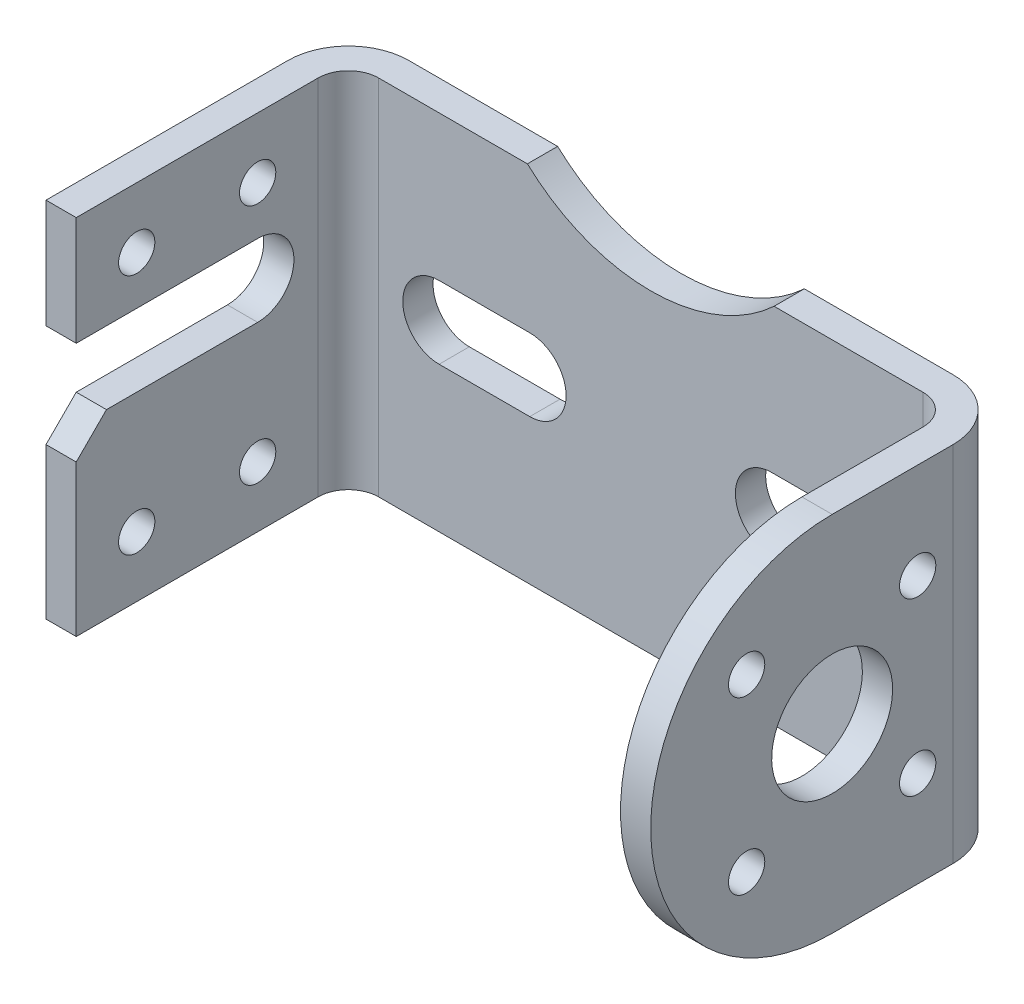
SolidWorks part; units mm, degrees
material "Nickel"
ref_plane "Front Plane" through (0, 0, 0) normal (0, 0, 1) x (1, 0, 0)
ref_plane "Top Plane" through (0, 0, 0) normal (0, 1, 0) x (1, 0, 0)
ref_plane "Right Plane" through (0, 0, 0) normal (1, 0, 0) x (0, 0, -1)
sketch "Sketch1" plane through (0, 0, 0) normal (0, 0, 1) x (1, 0, 0)
  line L1 (0, 0) -> (110, 0)
  line L2 (0, 0) -> (0, -60)
  line L3 (0, -60) -> (110, -60)
  line L4 (110, 0) -> (110, -60)
  dimension "D1" = 110
  dimension "D2" = 60
extrude "Boss-Extrude1" add sketch "Sketch1" along normal blind 50
sketch "Sketch2" plane through (0, 0, 50) normal (0, 0, 1) x (1, 0, 0)
  line L0 (110, 0) -> (0, 0) construction
  line L1 (5, 0) -> (105, 0)
  line L2 (5, 0) -> (5, -60)
  line L3 (5, -60) -> (105, -60)
  line L4 (105, 0) -> (105, -60)
  line L5 (0, -60) -> (110, -60) construction
  line L6 (110, -60) -> (110, 0) construction
  line L7 (0, 0) -> (0, -60) construction
  dimension "D1" = 5
  dimension "D2" = 5
extrude "Cut-Extrude1" cut sketch "Sketch2" against normal blind 45
fillet "Fillet1" radius 5 2 edges at (5, -30, 5) (105, -30, 5)
fillet "Fillet2" radius 10 2 edges at (110, -30, 0) (0, -30, 0)
sketch "Sketch3" plane through (0, 0, 5) normal (0, 0, 1) x (1, 0, 0)
  line L0 (100, 0) -> (10, 0) construction
  circle A0 centre (55, 22) radius 30
  dimension "D1" = 60
  dimension "D3" = 22
  dimension "D2" = 55
extrude "Cut-Extrude2" cut sketch "Sketch3" against normal through all
sketch "Sketch4" plane through (0, 0, 5) normal (0, 0, 1) x (1, 0, 0)
  line L0 (55, -8) -> (55, -70.5537) construction
  line L1 (20, -30) -> (35, -30) construction
  line L2 (20, -24) -> (35, -24)
  line L3 (20, -36) -> (35, -36)
  line L4 (10, -60) -> (100, -60) construction
  line L5 (90, -30) -> (75, -30) construction
  line L6 (90, -24) -> (75, -24)
  line L7 (90, -36) -> (75, -36)
  arc A0 (34.6039, 0) -> (75.3961, 0) centre (55, 22) ccw construction
  arc A1 (20, -24) -> (20, -36) centre (20, -30) ccw
  arc A2 (35, -36) -> (35, -24) centre (35, -30) ccw
  arc A3 (90, -24) -> (90, -36) centre (90, -30) cw
  arc A4 (75, -36) -> (75, -24) centre (75, -30) cw
  point P8 (27.5, -30)
  point P17 (82.5, -30)
  dimension "D3" = 6
  dimension "D1" = 15
  dimension "D2" = 20
  dimension "D4" = 30
extrude "Cut-Extrude3" cut sketch "Sketch4" against normal through all
sketch "Sketch5" plane through (0, 0, 0) normal (-1, 0, 0) x (0, 0, 1)
  line L0 (60, -24) -> (20, -24) construction
  line L1 (60, -30) -> (20, -30)
  line L2 (60, -18) -> (20, -18)
  line L3 (50, 0) -> (50, -60) construction
  line L5 (50, -30) -> (-1.733, -30) construction
  arc A0 (60, -30) -> (60, -18) centre (60, -24) ccw
  arc A1 (20, -18) -> (20, -30) centre (20, -24) ccw
  point P2 (40, -24)
  dimension "D1" = 6
  dimension "D2" = 30
  dimension "D3" = 40
extrude "Cut-Extrude4" cut sketch "Sketch5" against normal up to next
sketch "Sketch6" plane through (0, 0, 0) normal (-1, 0, 0) x (0, 0, 1)
  line L0 (30, 0) -> (30, -60) construction
  line L1 (50, 0) -> (10, 0) construction
  line L2 (50, -60) -> (10, -60) construction
  line L3 (0, -30) -> (52.0561, -30) construction
  line L4 (0, -60) -> (0, 0) construction
  line L5 (50, 0) -> (50, -18) construction
  circle A0 centre (20, -10) radius 3
  circle A1 centre (40, -10) radius 3
  circle A2 centre (40, -50) radius 3
  circle A3 centre (20, -50) radius 3
  dimension "D1" = 6
  dimension "D2" = 30
  dimension "D3" = 10
extrude "Cut-Extrude5" cut sketch "Sketch6" against normal up to next
sketch "Sketch8" plane through (110, 0, 0) normal (1, 0, 0) x (0, 0, -1)
  line L0 (-30, 0) -> (-30, -60) construction
  line L1 (-50, 0) -> (-10, 0) construction
  line L2 (-50, -60) -> (-10, -60) construction
  line L3 (-50, -30) -> (-10, -30) construction
  line L4 (-50, -60) -> (-50, 0) construction
  line L5 (-10, -60) -> (-10, 0) construction
  line L6 (-10, -7.6393) -> (-10, -52.3607)
  arc A1 (-10, -7.6393) -> (-10, -52.3607) centre (-30, -30) ccw
  dimension "D1" = 60
extrude "Boss-Extrude2" add sketch "Sketch8" against normal blind 5
sketch "Sketch9" plane through (110, 0, 0) normal (1, 0, 0) x (0, 0, -1)
  line L0 (-30, 0) -> (-30, -60) construction
  line L1 (-50, 0) -> (-10, 0) construction
  line L2 (-50, -60) -> (-10, -60) construction
  line L3 (-60, -30) -> (0, -30) construction
  line L4 (-50, -7.6393) -> (-50, 0)
  line L5 (-50, 0) -> (-30, 0)
  line L6 (-50, -60) -> (-30, -60)
  line L7 (-50, -52.3607) -> (-50, -60)
  arc A0 (-30, 0) -> (-50, -7.6393) centre (-30, -30) ccw
  arc A1 (-50, -52.3607) -> (-30, -60) centre (-30, -30) ccw
extrude "Cut-Extrude6" cut sketch "Sketch9" against normal up to next contours L5 A0 L4 | L7 L6 A1
sketch "Sketch10" plane through (110, 0, 0) normal (1, 0, 0) x (0, 0, -1)
  line L0 (-60, -30) -> (0, -30) construction
  line L1 (-30, 0) -> (-30, -60) construction
  line L2 (-30, -30) -> (-51.2132, -8.7868) construction
  arc A0 (-30, 0) -> (-30, -60) centre (-30, -30) ccw construction
  circle A1 centre (-30, -30) radius 10
  circle A2 centre (-30, -30) radius 20
  circle A3 centre (-44.1421, -15.8579) radius 3
  circle A4 centre (-15.8579, -15.8579) radius 3
  circle A5 centre (-15.8579, -44.1421) radius 3
  circle A6 centre (-44.1421, -44.1421) radius 3
  dimension "D1" = 20
  dimension "D2" = 40
  dimension "D4" = 6
  dimension "D3" = 45
extrude "Cut-Extrude9" cut sketch "Sketch10" against normal up to next contours A3 | A4 | A5 | A6 | A1
chamfer "Chamfer1" distance 5 angle 45 1 edges at (2.5, -30, 50)
